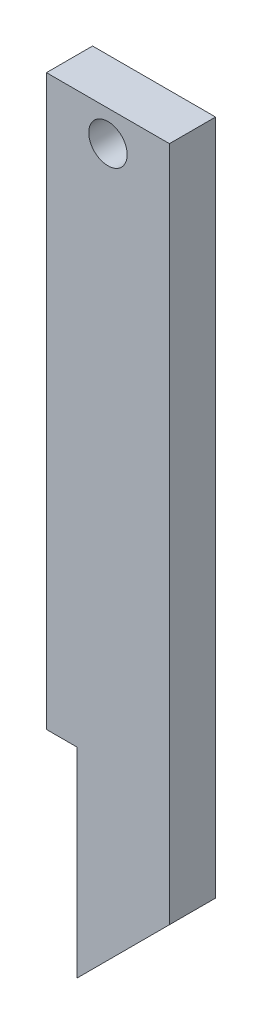
SolidWorks part; units mm, degrees
ref_plane "Front Plane" through (0, 0, 0) normal (0, 0, 1) x (1, 0, 0)
ref_plane "Top Plane" through (0, 0, 0) normal (0, 1, 0) x (1, 0, 0)
ref_plane "Right Plane" through (0, 0, 0) normal (1, 0, 0) x (0, 0, -1)
sketch "Sketch1" plane through (0, 0, 0) normal (0, 0, 1) x (1, 0, 0)
  line L0 (-9.5535, 42.9623) -> (-9.5535, -1.0377)
  line L1 (-17.5535, 42.9623) -> (-9.5535, 42.9623)
  line L2 (-17.5535, 42.9623) -> (-17.5535, -9.0377)
  line L3 (-17.5535, -9.0377) -> (-9.5535, -1.0377)
extrude "Boss-Extrude1" add sketch "Sketch1" along normal blind 3
sketch "Sketch2" plane through (0, 0, 3) normal (0, 0, 1) x (1, 0, 0)
  line L1 (-17.5535, -9.0377) -> (-17.5535, 5.9623)
  line L2 (-17.5535, 42.9623) -> (-17.5535, -9.0377) construction
  line L3 (-17.5535, 5.9623) -> (-15.5535, 5.9623)
  line L4 (-15.5535, 5.9623) -> (-15.5535, -7.0377)
  line L5 (-17.5535, -9.0377) -> (-9.5535, -1.0377) construction
  line L6 (-15.5535, -7.0377) -> (-17.5535, -9.0377)
  line L8 (-9.5535, 42.9623) -> (-17.5535, 42.9623) construction
  circle A0 centre (-13.5535, 40.9623) radius 1.25
  dimension "D1" = 2
extrude "Cut-Extrude1" cut sketch "Sketch2" against normal blind 3
